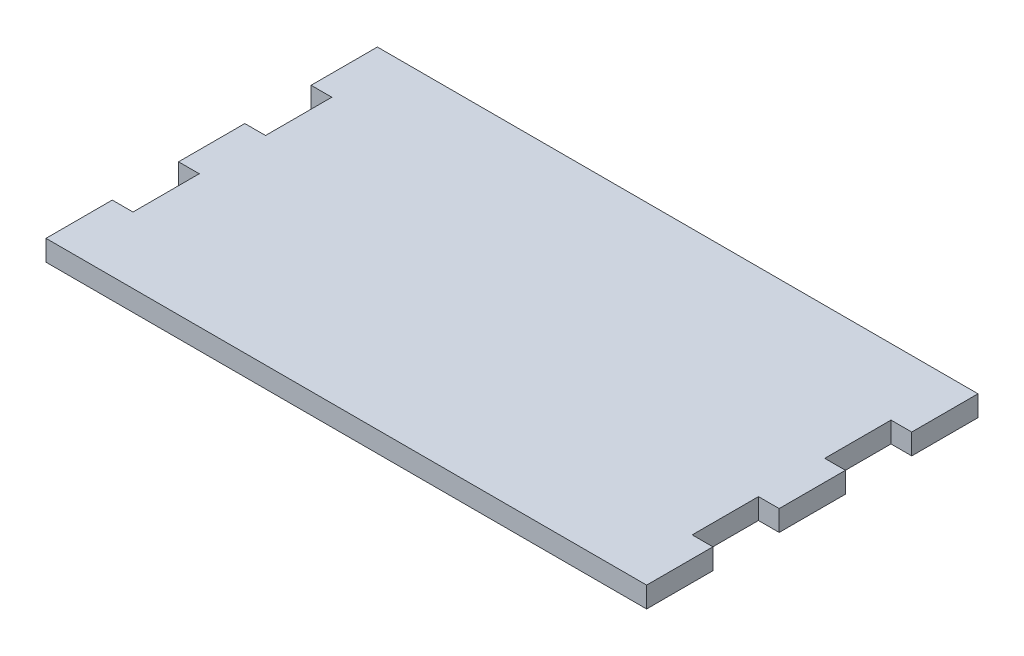
SolidWorks part; units mm, degrees
ref_plane "Front Plane" through (0, 0, 0) normal (0, 0, 1) x (1, 0, 0)
ref_plane "Top Plane" through (0, 0, 0) normal (0, 1, 0) x (1, 0, 0)
ref_plane "Right Plane" through (0, 0, 0) normal (1, 0, 0) x (0, 0, -1)
sketch "Sketch1" plane through (0, 0, 0) normal (0, 1, 0) x (1, 0, 0)
  line L0 (-67.5, 24) -> (-67.5, 8)
  line L1 (-72.5, 40) -> (72.5, 40)
  line L2 (-72.5, 40) -> (-72.5, 24)
  line L3 (-72.5, -40) -> (72.5, -40)
  line L4 (72.5, 40) -> (72.5, 24)
  line L5 (-72.5, 40) -> (72.5, -40) construction
  line L6 (-72.5, -40) -> (72.5, 40) construction
  line L7 (72.5, 8) -> (72.5, -8)
  line L9 (-72.5, 8) -> (-72.5, -8)
  line L11 (-72.5, -24) -> (-72.5, -40)
  line L12 (67.5, 24) -> (67.5, 8)
  line L13 (72.5, -24) -> (72.5, -40)
  line L15 (67.5, -8) -> (67.5, -24)
  line L17 (-72.5, 24) -> (-67.5, 24)
  line L18 (-72.5, 8) -> (-67.5, 8)
  line L19 (-72.5, -8) -> (-67.5, -8)
  line L20 (-72.5, -24) -> (-67.5, -24)
  line L21 (67.5, 24) -> (72.5, 24)
  line L22 (67.5, 8) -> (72.5, 8)
  line L23 (67.5, -8) -> (72.5, -8)
  line L24 (67.5, -24) -> (72.5, -24)
  line L26 (-67.5, -8) -> (-67.5, -24)
  point P0 (0, 0)
  dimension "D1" = 145
  dimension "D2" = 80
  dimension "D3" = 5
extrude "Boss-Extrude1" add sketch "Sketch1" along normal blind 5
